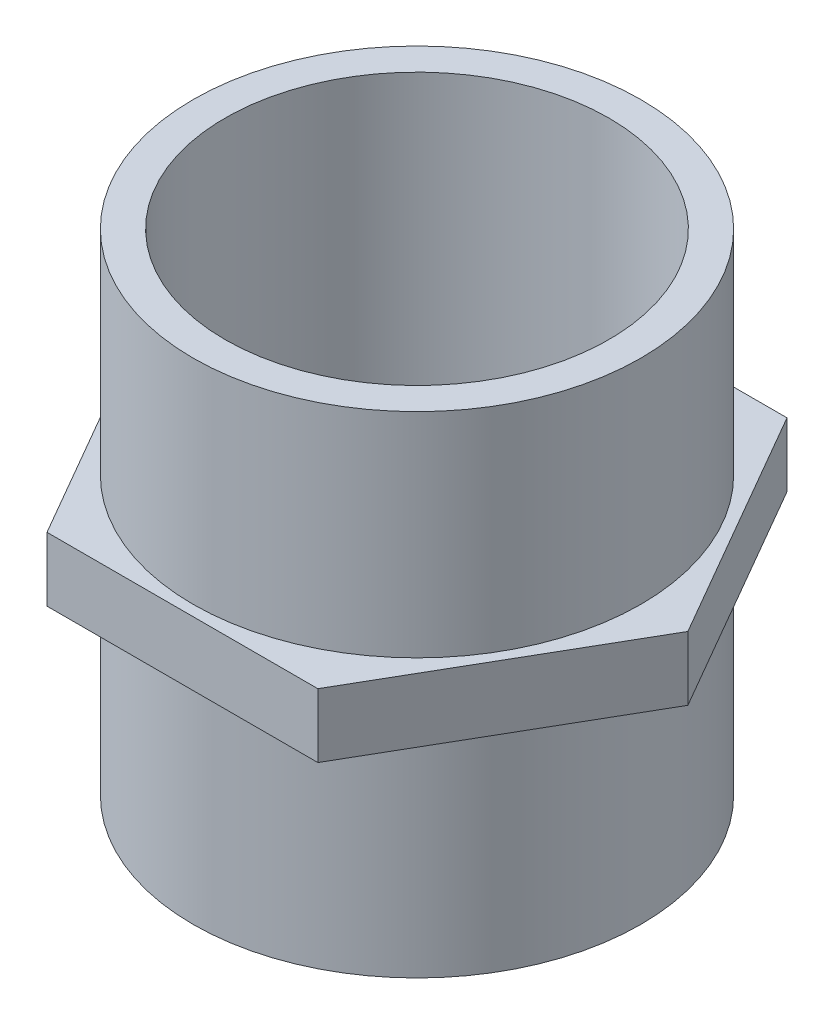
SolidWorks part; units mm, degrees
ref_plane "Front Plane" through (0, 0, 0) normal (0, 0, 1) x (1, 0, 0)
ref_plane "Top Plane" through (0, 0, 0) normal (0, 1, 0) x (1, 0, 0)
ref_plane "Right Plane" through (0, 0, 0) normal (1, 0, 0) x (0, 0, -1)
sketch "Sketch1" plane through (0, 0, 0) normal (0, 1, 0) x (1, 0, 0)
  line L1 (6.3509, -11) -> (12.7017, 0)
  line L2 (12.7017, 0) -> (6.3509, 11)
  line L3 (6.3509, 11) -> (-6.3509, 11)
  line L4 (-6.3509, 11) -> (-12.7017, 0)
  line L5 (-12.7017, 0) -> (-6.3509, -11)
  line L6 (-6.3509, -11) -> (6.3509, -11)
  circle A0 centre (0, 0) radius 11 construction
  dimension "D1" = 22
extrude "Boss-Extrude1" add sketch "Sketch1" along normal mid plane 3
sketch "Sketch2" plane through (0, 1.5, 0) normal (0, 1, 0) x (1, 0, 0)
  circle A0 centre (0, 0) radius 10.5
  dimension "D1" = 21
extrude "Boss-Extrude2" add sketch "Sketch2" along normal blind 10
mirror "Mirror1" about plane through (0, 0, 0) normal (0, 1, 0) of "Boss-Extrude2"
sketch "Sketch3" plane through (0, 11.5, 0) normal (0, 1, 0) x (1, 0, 0)
  circle A0 centre (0, 0) radius 9
  dimension "D1" = 18
extrude "Cut-Extrude1" cut sketch "Sketch3" against normal through all
